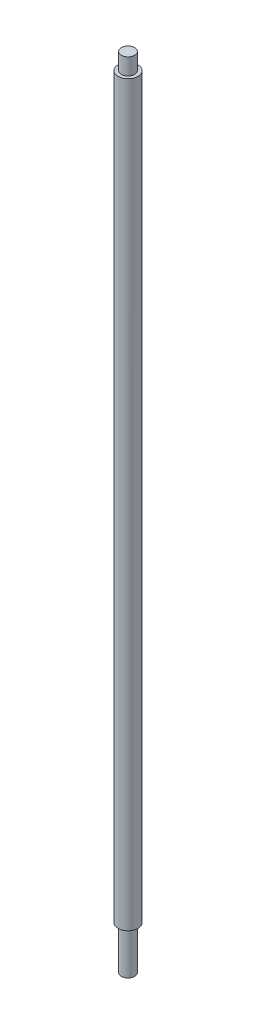
SolidWorks part; units mm, degrees
material "AISI 1020 Steel, Cold Rolled"
ref_plane "Front Plane" through (0, 0, 0) normal (0, 0, 1) x (1, 0, 0)
ref_plane "Top Plane" through (0, 0, 0) normal (0, 1, 0) x (1, 0, 0)
ref_plane "Right Plane" through (0, 0, 0) normal (1, 0, 0) x (0, 0, -1)
sketch "Sketch1" plane through (0, 0, 0) normal (0, 1, 0) x (1, 0, 0)
  circle A0 centre (0, 0) radius 6
  dimension "D1" = 12
extrude "Boss-Extrude1" add sketch "Sketch1" along normal mid plane 480
cosmetic thread "Cosmetic Thread3" parameters "D2"=10.344
sketch "Sketch2" plane through (0, 240, 0) normal (0, 1, 0) x (1, 0, 0)
  circle A0 centre (0, 0) radius 4
  circle A1 centre (0, 0) radius 6
  dimension "D1" = 8
extrude "Cut-Extrude1" cut sketch "Sketch2" against normal blind 10
sketch "Sketch3" plane through (0, -240, 0) normal (0, -1, 0) x (1, 0, 0)
  circle A0 centre (0, 0) radius 4
  circle A1 centre (0, 0) radius 6
  dimension "D1" = 8
  dimension "D2" = 12
extrude "Cut-Extrude2" cut sketch "Sketch3" against normal blind 26
